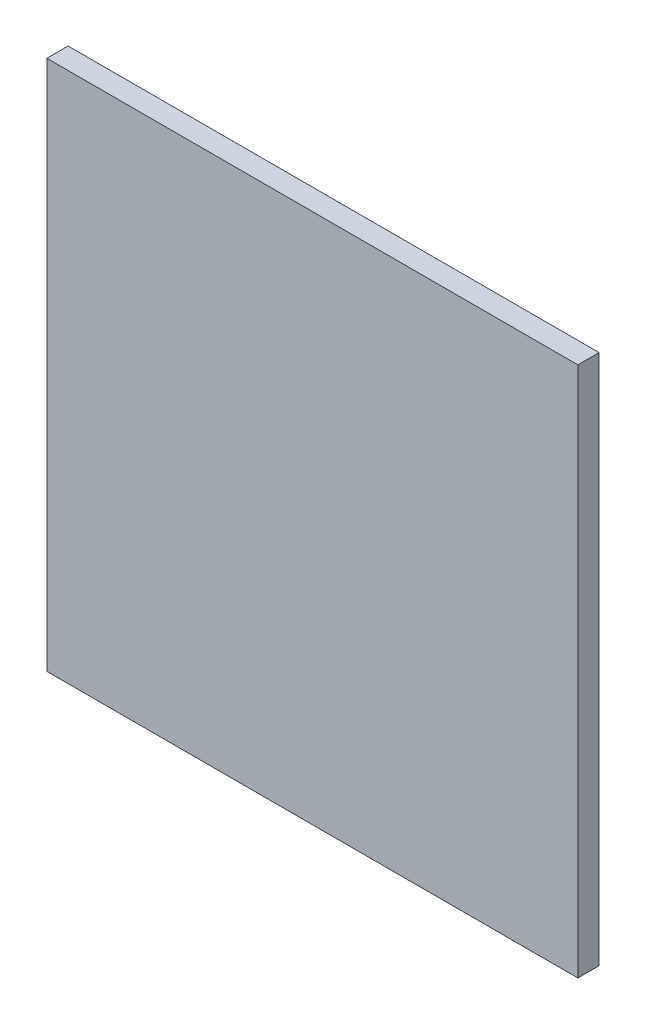
SolidWorks part; units mm, degrees
material "1.0116 (S235J2G3)"
ref_plane "Ebene vorne" through (0, 0, 0) normal (0, 0, 1) x (1, 0, 0)
ref_plane "Ebene oben" through (0, 0, 0) normal (0, 1, 0) x (1, 0, 0)
ref_plane "Ebene rechts" through (0, 0, 0) normal (1, 0, 0) x (0, 0, -1)
sketch "Skizze1" plane through (0, 0, 0) normal (0, 0, 1) x (1, 0, 0)
  line L1 (250, -250) -> (-250, -250)
  line L2 (250, -250) -> (250, 250)
  line L3 (250, 250) -> (-250, 250)
  line L4 (-250, -250) -> (-250, 250)
  line L5 (250, -250) -> (-250, 250) construction
  line L6 (250, 250) -> (-250, -250) construction
  point P0 (0, 0)
  dimension "D1" = 500
  dimension "D2" = 500
extrude "Aufsatz-Linear austragen1" add sketch "Skizze1" along normal blind 20
